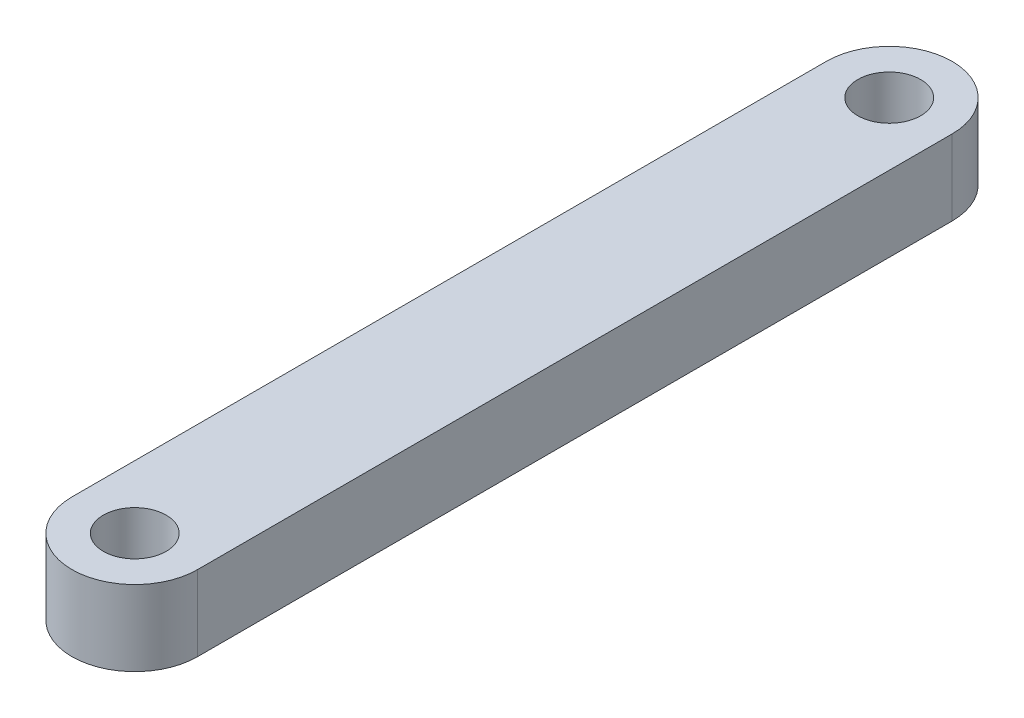
SolidWorks part; units mm, degrees
ref_plane "Front Plane" through (0, 0, 0) normal (0, 0, 1) x (1, 0, 0)
ref_plane "Top Plane" through (0, 0, 0) normal (0, 1, 0) x (1, 0, 0)
ref_plane "Right Plane" through (0, 0, 0) normal (1, 0, 0) x (0, 0, -1)
ref_plane "Plane1" through (0, 2.5, 0) normal (0, 1, 0) x (1, 0, 0)
sketch "Sketch1" plane through (0, 2.5, 0) normal (0, 1, 0) x (1, 0, 0)
  line L0 (-2.5, -48.6623) -> (-2.5, -18.6623)
  line L1 (-7.5, -18.6623) -> (-7.5, -48.6623)
  circle A0 centre (-5, -48.6623) radius 1
  arc A1 (-7.5, -48.6623) -> (-2.5, -48.6623) centre (-5, -48.6623) ccw
  arc A2 (-2.5, -18.6623) -> (-7.5, -18.6623) centre (-5, -18.6623) ccw
  circle A3 centre (-5, -18.6623) radius 1
extrude "Boss-Extrude1" add sketch "Sketch1" against normal blind 3
sketch "Sketch2" plane through (0, -0.5, 0) normal (0, -1, 0) x (1, 0, 0)
  line L2 (-7.5, 48.6623) -> (-7.5, 18.6623)
  line L3 (-2.5, 18.6623) -> (-2.5, 48.6623)
  line L4 (-7.5, 48.6623) -> (-7.5, 18.6623)
  line L5 (-2.5, 18.6623) -> (-2.5, 48.6623)
  circle A1 centre (-5, 18.6623) radius 1.25
  arc A2 (-2.5, 48.6623) -> (-7.5, 48.6623) centre (-5, 48.6623) ccw
  arc A3 (-7.5, 18.6623) -> (-2.5, 18.6623) centre (-5, 18.6623) ccw
  arc A4 (-2.5, 48.6623) -> (-7.5, 48.6623) centre (-5, 48.6623) ccw
  arc A5 (-7.5, 18.6623) -> (-2.5, 18.6623) centre (-5, 18.6623) ccw
  dimension "D2" = 2.5
  dimension "D1" = 0
extrude "Cut-Extrude1" cut sketch "Sketch2" against normal through all contours A1
sketch "Sketch3" plane through (0, -0.5, 0) normal (0, -1, 0) x (1, 0, 0)
  circle A0 centre (-5, 48.6623) radius 1.25
  dimension "D1" = 2.5
extrude "Cut-Extrude2" cut sketch "Sketch3" against normal through all
